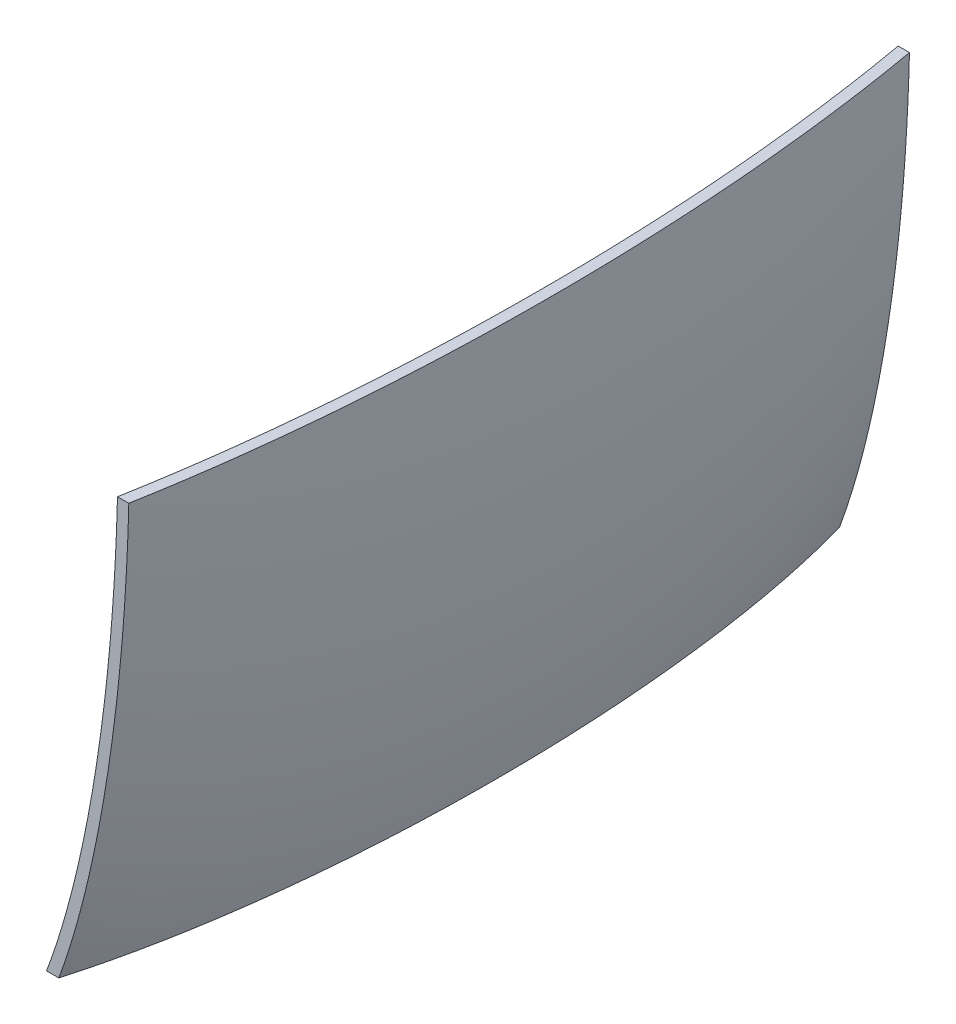
SolidWorks part; units mm, degrees
ref_plane "Front Plane" through (0, 0, 0) normal (0, 0, 1) x (1, 0, 0)
ref_plane "Top Plane" through (0, 0, 0) normal (0, 1, 0) x (1, 0, 0)
ref_plane "Right Plane" through (0, 0, 0) normal (1, 0, 0) x (0, 0, -1)
sketch "Sketch0" plane through (0, 0, 0) normal (0, 0, 1) x (1, 0, 0)
  line L0 (-78.994, 0) -> (0, 0) construction
  line L2 (-19.558, 0) -> (0, 0) construction
  line L4 (-78.994, 66.929) -> (-78.994, -66.929) construction
  line L5 (-19.558, 57.0357) -> (-78.994, 57.3786) construction
  line L6 (-19.558, 57.0357) -> (-19.558, -57.0357) construction
  line L7 (-19.558, -57.0357) -> (-78.994, -57.3786) construction
  line L8 (-78.994, 57.3786) -> (-78.994, -57.3786) construction
  line L14 (-19.558, 48.5902) -> (-19.558, -48.5902) construction
  dimension "M" = 133.858
  dimension "OD A" = 114.7572
  dimension "OD B" = 114.0714
  dimension "ID" = 97.1804
  dimension "W" = 78.994
  dimension "C" = 59.436
sketch "Sketch1" plane through (0, 0, 0) normal (0, 0, 1) x (1, 0, 0)
  line L0 (-78.994, 0) -> (0, 0) construction
  line L1 (-78.994, 0) -> (0, 0) construction
  line L2 (-19.558, 0) -> (0, 0) construction
  line L3 (-78.994, -66.929) -> (-19.558, -66.929)
  line L4 (-78.994, -66.929) -> (-78.994, -57.3786)
  line L5 (-78.994, -57.3786) -> (-19.558, -57.0357)
  line L6 (-19.558, 0) -> (-19.558, -57.0357) construction
  line L7 (-19.558, -57.0357) -> (-19.558, -66.929) construction
  line L8 (-9.8933, 0) -> (0, 0)
  line L9 (1, 0) -> (0, 0)
  line L10 (-19.558, -66.929) -> (-19.558, -67.929)
  ellipse E0 centre (-19.558, 0) end of major axis (-19.558, 66.929) minor radius 19.558 (-19.558, -66.929) -> (0, 0) ccw
  ellipse E1 centre (-19.558, 0) end of major axis (-19.558, -57.0357) minor radius 9.6647 (-19.558, -57.0357) -> (-9.8933, 0) ccw
  spline S0 degree 1 poles (-19.558, -67.929) (1, 0) knots 0 0 1 1 construction
  spline S1 degree 3 poles (-19.558, -67.929) (-18.8021, -67.929) (-17.3052, -67.6735) (-14.4426, -66.2094) (-11.1865, -62.793) (-7.6982, -56.4003) (-4.6762, -47.9065) (-2.2083, -37.6123) (-0.3786, -25.8967) (0.5591, -15.3141) (0.9368, -6.6009) (1, -2.1965) (1, 0) knots -3.141593 -3.141593 -3.141593 -3.141593 -3.043418 -2.945243 -2.748894 -2.552544 -2.356194 -2.159845 -1.963495 -1.767146 -1.668971 -1.570796 -1.570796 -1.570796 -1.570796
  dimension "D1" = 1
revolve "Revolve1" add sketch "Sketch1" angle 360 about L1
sketch "Sketch2" plane through (0, 0, 0) normal (1, 0, 0) x (0, 0, -1)
  line L1 (35, -45) -> (-35, -45)
  line L2 (35, -45) -> (35, -5)
  line L3 (35, -5) -> (-35, -5)
  line L4 (-35, -45) -> (-35, -5)
  line L5 (35, -45) -> (-35, -5) construction
  line L6 (35, -5) -> (-35, -45) construction
  line L7 (100, 100) -> (-100, 100)
  line L8 (100, 100) -> (100, -100)
  line L9 (100, -100) -> (-100, -100)
  line L10 (-100, 100) -> (-100, -100)
  line L11 (100, 100) -> (-100, -100) construction
  line L12 (100, -100) -> (-100, 100) construction
  point P0 (0, -25)
  point P5 (0, 0)
  dimension "D1" = 25
  dimension "D2" = 40
  dimension "D3" = 70
  dimension "D4" = 200
  dimension "D5" = 200
extrude "Cut-Extrude1" cut sketch "Sketch2" against normal through all both and the other way through all
